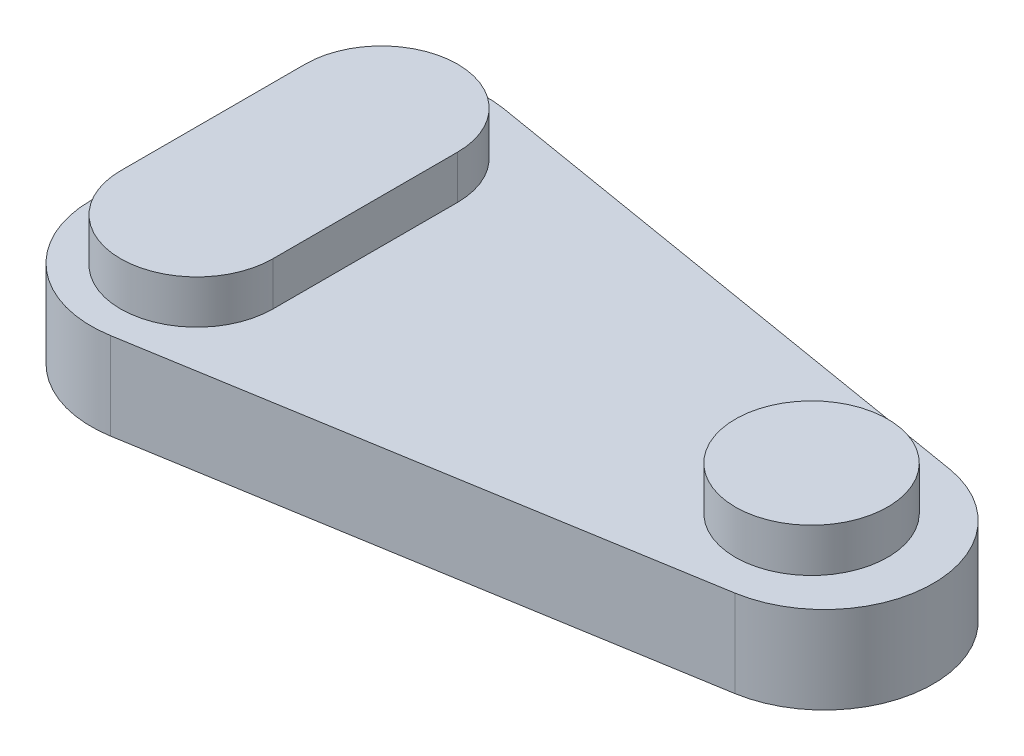
SolidWorks part; units mm, degrees
ref_plane "Front Plane" through (0, 0, 0) normal (0, 0, 1) x (1, 0, 0)
ref_plane "Top Plane" through (0, 0, 0) normal (0, 1, 0) x (1, 0, 0)
ref_plane "Right Plane" through (0, 0, 0) normal (1, 0, 0) x (0, 0, -1)
sketch "Sketch1" plane through (0, 0, 0) normal (0, 1, 0) x (1, 0, 0)
  line L0 (0, 7.4959) -> (0, 17.9041)
  line L1 (0, 12.7) -> (76.2, 12.7) construction
  line L2 (7.3939, 24.1677) -> (38.6184, 18.9636)
  line L3 (38.6184, 6.4364) -> (7.3939, 1.2323)
  arc A0 (38.6184, 6.4364) -> (38.6184, 18.9636) centre (37.5745, 12.7) ccw
  arc A1 (0, 17.9041) -> (7.3939, 24.1677) centre (6.35, 17.9041) cw
  arc A2 (0, 7.4959) -> (7.3939, 1.2323) centre (6.35, 7.4959) ccw
  point P10 (0, 25.4)
  point P13 (0, 0)
  dimension "D3" = 6.35
  dimension "D1" = 25.4
  dimension "D2" = 76.2
extrude "Boss-Extrude1" add sketch "Sketch1" along normal blind 5.08 contours L3 A2 L0 A1 L2 A0
sketch3d "3DSketch1"
  line L0 (0, 5.08, -12.7) -> (43.9245, 5.08, -12.7) construction
  line L1 (0, 5.08, -7.4959) -> (0, 5.08, -17.9041) construction
  arc A0 (38.6184, 5.08, -6.4364) -> (38.6184, 5.08, -18.9636) centre (37.5745, 5.08, -12.7) ccw construction
  point P7 (37.5745, 11.43, -12.7)
sketch "Sketch5" plane through (0, 5.08, 0) normal (0, 1, 0) x (1, 0, 0)
  line L0 (0, 12.7) -> (43.9245, 12.7) construction
  line L1 (6.35, 18.0864) -> (6.35, 7.3136) construction
  line L2 (10.795, 18.0864) -> (10.795, 7.3136)
  line L3 (1.905, 18.0864) -> (1.905, 7.3136)
  arc A0 (10.795, 18.0864) -> (1.905, 18.0864) centre (6.35, 18.0864) ccw
  arc A1 (1.905, 7.3136) -> (10.795, 7.3136) centre (6.35, 7.3136) ccw
  circle A2 centre (36.83, 12.7) radius 4.445
  point P6 (6.35, 12.7)
  dimension "D2" = 4.445
  dimension "D4" = 8.89
  dimension "D1" = 6.35
  dimension "D3" = 30.48
extrude "Boss-Extrude2" add sketch "Sketch5" along normal blind 2.54 contours L3 A1 L2 A0 | A2
